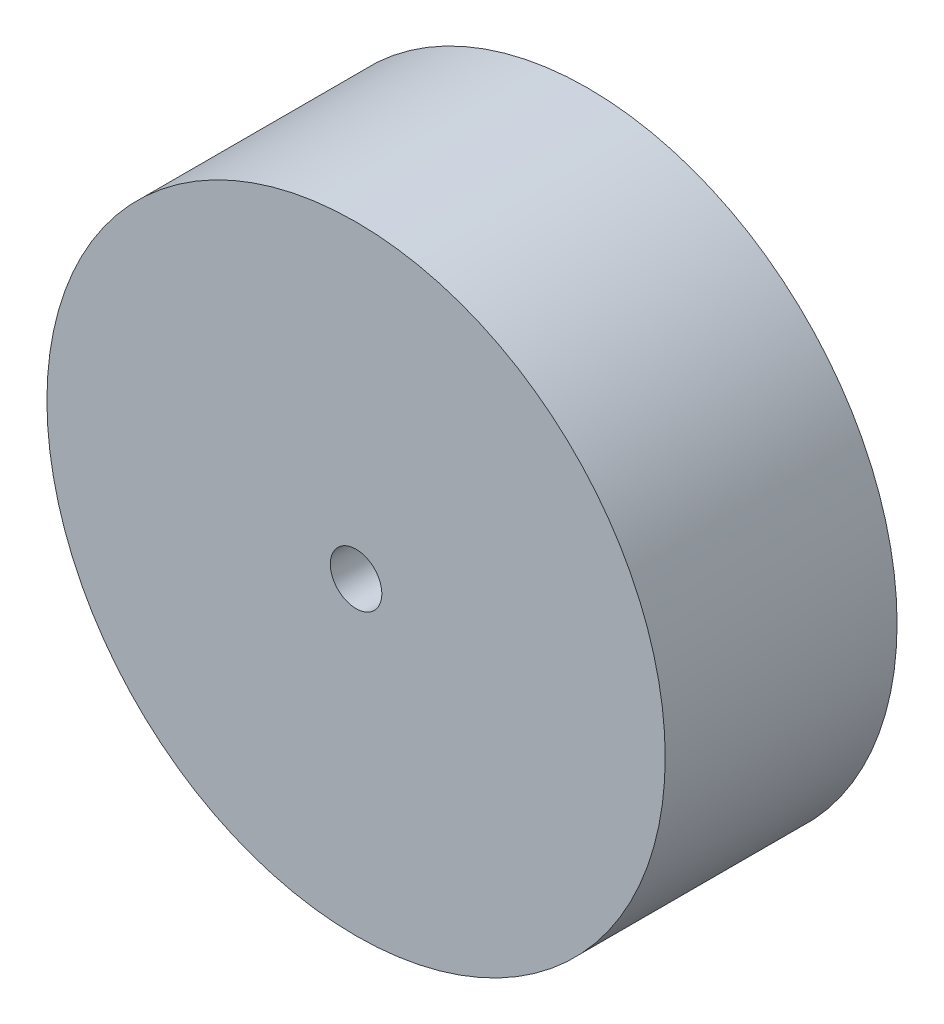
SolidWorks part; units mm, degrees
ref_plane "Plan de face" through (0, 0, 0) normal (0, 0, 1) x (1, 0, 0)
ref_plane "Plan de dessus" through (0, 0, 0) normal (0, 1, 0) x (1, 0, 0)
ref_plane "Plan de droite" through (0, 0, 0) normal (1, 0, 0) x (0, 0, -1)
sketch "Esquisse1" plane through (0, 0, 0) normal (0, 0, 1) x (1, 0, 0)
  circle A0 centre (0, 0) radius 36
extrude "Boss.-Extru.1" add sketch "Esquisse1" along normal blind 27
sketch "Esquisse2" plane through (0, 0, 27) normal (0, 0, 1) x (1, 0, 0)
  circle A0 centre (0, 0) radius 3
extrude "Enlèv. mat.-Extru.1" cut sketch "Esquisse2" against normal blind 27
